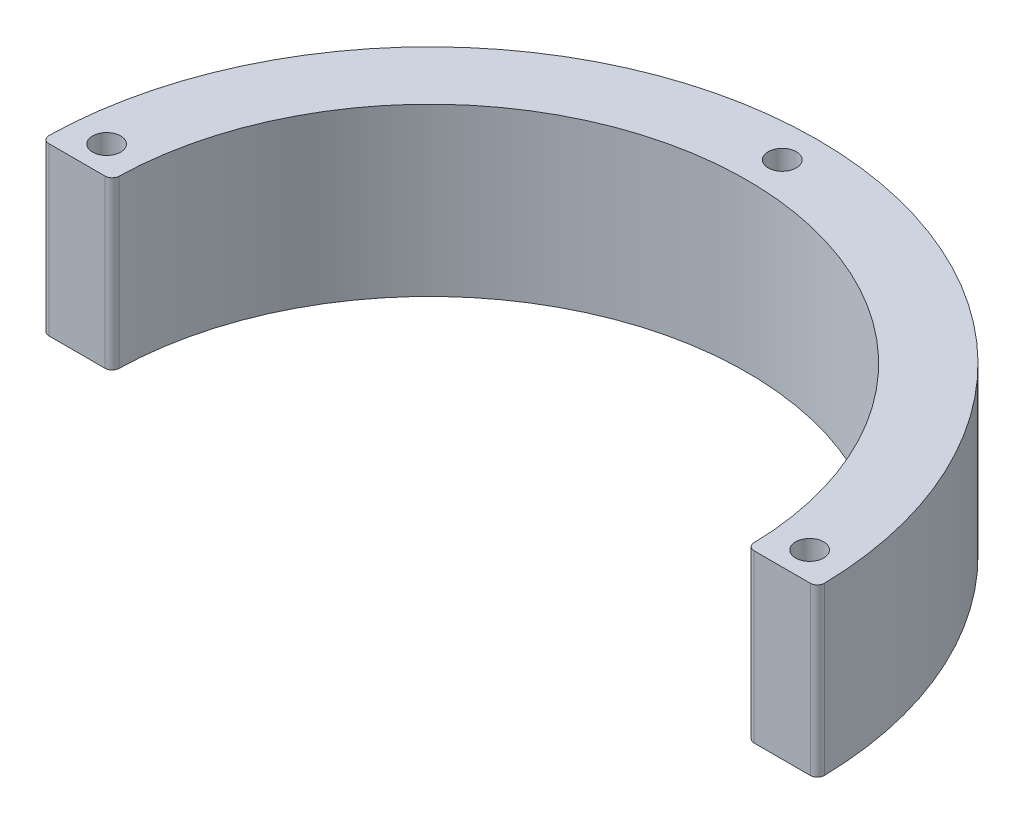
SolidWorks part; units mm, degrees
ref_plane "前视基准面" through (0, 0, 0) normal (0, 0, 1) x (1, 0, 0)
ref_plane "上视基准面" through (0, 0, 0) normal (0, 1, 0) x (1, 0, 0)
ref_plane "右视基准面" through (0, 0, 0) normal (1, 0, 0) x (0, 0, -1)
sketch "草图1" plane through (0, 0, 0) normal (0, 1, 0) x (1, 0, 0)
  line L0 (-27.6, 0) -> (-22.6, 0)
  line L1 (22.6, 0) -> (27.6, 0)
  arc A0 (27.6, 0) -> (-27.6, 0) centre (0, 0) ccw
  arc A1 (22.6, 0) -> (-22.6, 0) centre (0, 0) ccw
  circle A3 centre (0, 0) radius 22.6 construction
  circle A4 centre (0, 0) radius 27.6 construction
  point P7 (22.6, 0)
  point P10 (26.394, 8.0695)
  dimension "D1" = 55.2
  dimension "D2" = 5
extrude "凸台-拉伸1" add sketch "草图1" along normal blind 11.85
sketch "草图2" plane through (0, 11.85, 0) normal (0, 1, 0) x (1, 0, 0)
  line L1 (-27.6, 0) -> (0, 0) construction
  line L2 (-25.0177, 2.0305) -> (0, 0) construction
  line L3 (0, 0) -> (25.0177, 2.0305) construction
  line L4 (0, 0) -> (0, 25.1) construction
  circle A2 centre (0, 0) radius 25.1 construction
  circle A3 centre (-25.0177, 2.0305) radius 1
  circle A4 centre (25.0177, 2.0305) radius 1
  circle A5 centre (0, 25.1) radius 1
  dimension "D1" = 50.2
  dimension "D2" = 2
  dimension "D4" = 2
  dimension "D5" = 2
  dimension "D3" = 4.64
  dimension "D6" = 85.36
extrude "切除-拉伸1" cut sketch "草图2" against normal through all
fillet "圆角1" radius 0.5 4 edges at (27.6, 5.925, 0) (22.6, 5.925, 0) (-22.6, 5.925, 0) (-27.6, 5.925, 0)
